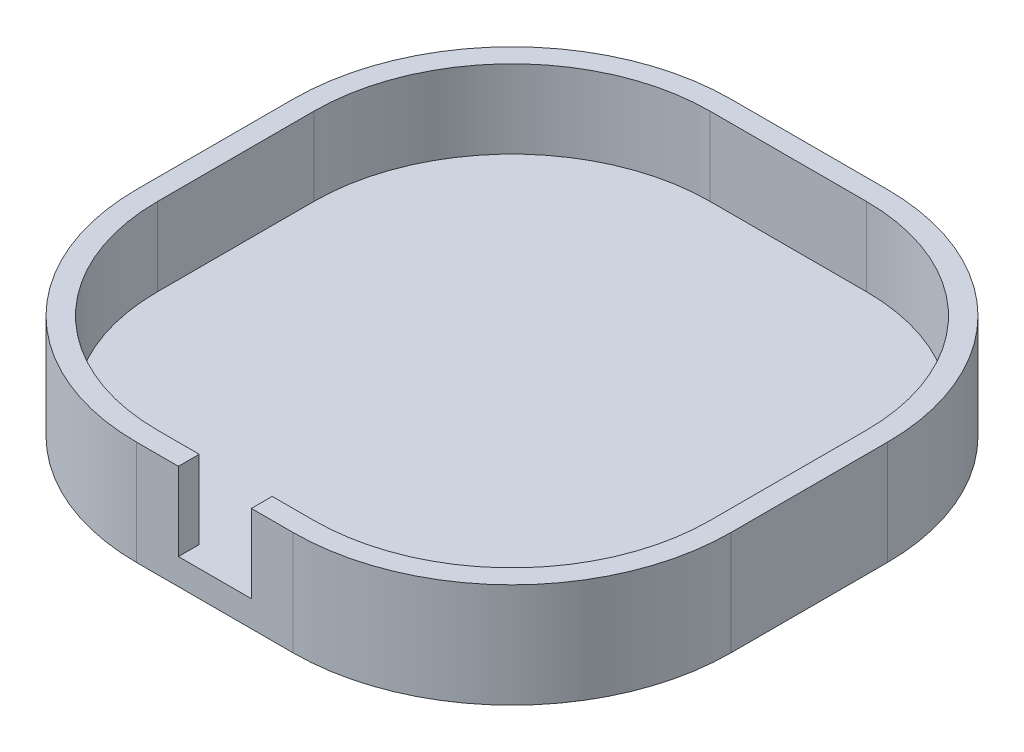
SolidWorks part; units mm, degrees
ref_plane "Front Plane" through (0, 0, 0) normal (0, 0, 1) x (1, 0, 0)
ref_plane "Top Plane" through (0, 0, 0) normal (0, 1, 0) x (1, 0, 0)
ref_plane "Right Plane" through (0, 0, 0) normal (1, 0, 0) x (0, 0, -1)
sketch "Sketch1" plane through (0, 0, 0) normal (0, 1, 0) x (1, 0, 0)
  line L1 (-15, -57) -> (15, -57)
  line L6 (-57, -15) -> (-57, 15)
  line L7 (-15, 57) -> (15, 57)
  line L8 (57, -15) -> (57, 15)
  line L9 (-57, -57) -> (57, 57) construction
  line L10 (-57, 57) -> (57, -57) construction
  arc A0 (-57, 15) -> (-15, 57) centre (-15, 15) cw
  arc A1 (57, 15) -> (15, 57) centre (15, 15) ccw
  arc A2 (-15, -57) -> (-57, -15) centre (-15, -15) cw
  arc A3 (57, -15) -> (15, -57) centre (15, -15) cw
  point P0 (0, 0)
  dimension "D3" = 42
  dimension "D4" = 42
  dimension "D5" = 42
  dimension "D6" = 42
  dimension "D1" = 114
  dimension "D2" = 114
extrude "Boss-Extrude1" add sketch "Sketch1" along normal blind 5
sketch "Sketch2" plane through (0, 5, 0) normal (0, 1, 0) x (1, 0, 0)
  line L1 (57, -15) -> (57, 15) construction
  line L2 (-15, -57) -> (15, -57) construction
  line L14 (-57, 15) -> (-57, -15) construction
  line L15 (15, 57) -> (-15, 57) construction
  line L16 (57, -15) -> (57, 15)
  line L17 (-15, -57) -> (15, -57)
  line L18 (-57, 15) -> (-57, -15)
  line L19 (15, 57) -> (-15, 57)
  line L20 (-53, 15) -> (-53, -15)
  line L21 (-15, -53) -> (15, -53)
  line L22 (53, -15) -> (53, 15)
  line L23 (15, 53) -> (-15, 53)
  arc A1 (57, 15) -> (15, 57) centre (15, 15) ccw construction
  arc A12 (15, -57) -> (57, -15) centre (15, -15) ccw construction
  arc A13 (-57, -15) -> (-15, -57) centre (-15, -15) ccw construction
  arc A14 (-15, 57) -> (-57, 15) centre (-15, 15) ccw construction
  arc A15 (57, 15) -> (15, 57) centre (15, 15) ccw
  arc A16 (15, -57) -> (57, -15) centre (15, -15) ccw
  arc A17 (-57, -15) -> (-15, -57) centre (-15, -15) ccw
  arc A18 (-15, 57) -> (-57, 15) centre (-15, 15) ccw
  arc A19 (-15, 53) -> (-53, 15) centre (-15, 15) ccw
  arc A20 (-53, -15) -> (-15, -53) centre (-15, -15) ccw
  arc A21 (15, -53) -> (53, -15) centre (15, -15) ccw
  arc A22 (53, 15) -> (15, 53) centre (15, 15) ccw
  dimension "D1" = 4
extrude "Boss-Extrude2" add sketch "Sketch2" along normal blind 15
sketch "Sketch3" plane through (0, 20, 0) normal (0, 1, 0) x (1, 0, 0)
  line L0 (-15, -53) -> (15, -53) construction
  line L1 (-7, -53) -> (7, -53)
  line L2 (-7, -53) -> (-7, -57)
  line L3 (-7, -57) -> (7, -57)
  line L4 (7, -53) -> (7, -57)
  line L5 (-15, -57) -> (15, -57) construction
  line L6 (57, -15) -> (57, 15) construction
  line L7 (-57, 15) -> (-57, -15) construction
  dimension "D1" = 50
  dimension "D2" = 50
extrude "Cut-Extrude1" cut sketch "Sketch3" against normal up to surface (15 mm away) up to face at (0, 5, 0)
